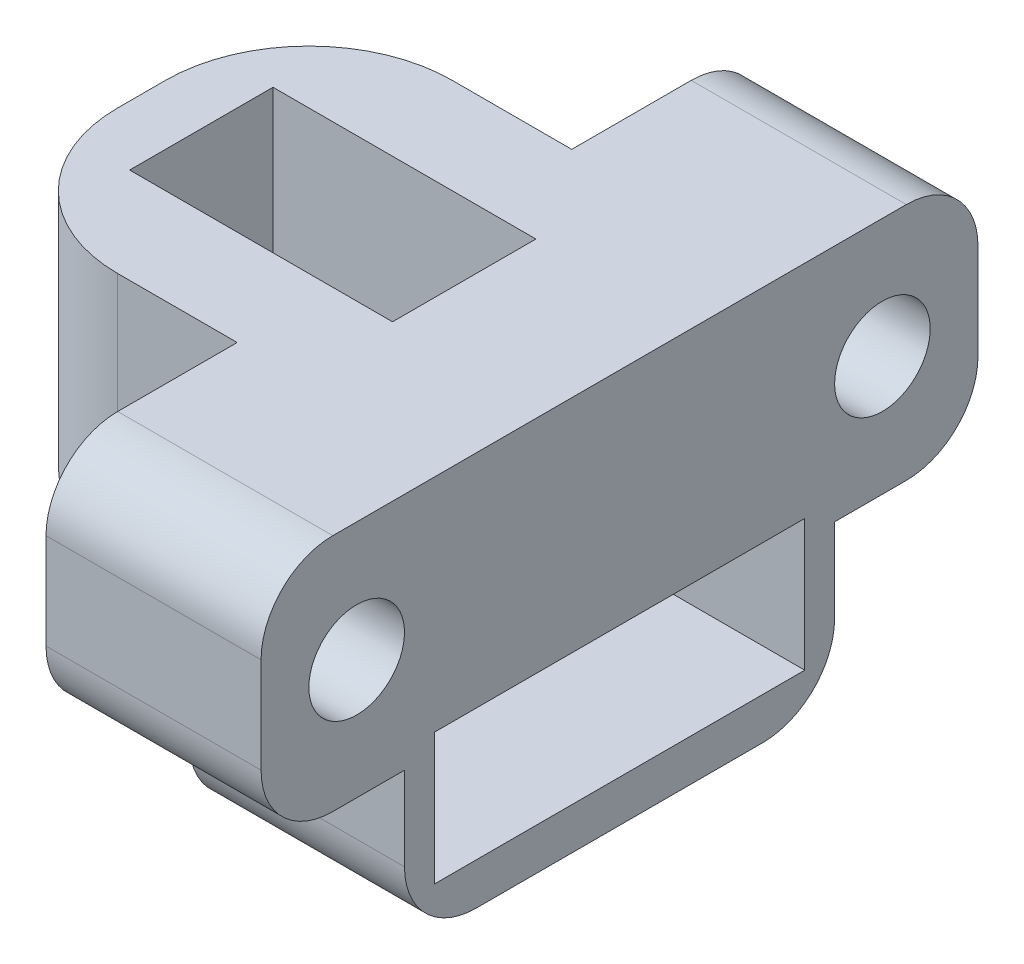
SolidWorks part; units mm, degrees
ref_plane "Plano frontal" through (0, 0, 0) normal (0, 0, 1) x (1, 0, 0)
ref_plane "Plano superior" through (0, 0, 0) normal (0, 1, 0) x (1, 0, 0)
ref_plane "Plano direito" through (0, 0, 0) normal (1, 0, 0) x (0, 0, -1)
sketch "Esboço1" plane through (0, 0, 0) normal (0, 1, 0) x (1, 0, 0)
  line L1 (-10, 15) -> (10, 15)
  line L2 (-10, 15) -> (-10, -15)
  line L3 (-10, -15) -> (10, -15)
  line L4 (10, 15) -> (10, -15)
  line L5 (-10, 15) -> (10, -15) construction
  line L6 (-10, -15) -> (10, 15) construction
  point P0 (0, 0)
  dimension "D1" = 30
  dimension "D2" = 20
extrude "Ressalto-extrusão1" add sketch "Esboço1" along normal blind 10
sketch "Esboço2" plane through (0, 10, 0) normal (0, 1, 0) x (1, 0, 0)
  line L1 (-10, 15) -> (1, 15)
  line L2 (-10, 15) -> (-10, 7)
  line L3 (-10, 7) -> (1, 7)
  line L4 (1, 15) -> (1, 7)
  line L5 (-10, -15) -> (1, -15)
  line L6 (-10, -15) -> (-10, -7)
  line L7 (-10, -7) -> (1, -7)
  line L8 (1, -15) -> (1, -7)
  dimension "D1" = 8
  dimension "D2" = 8
  dimension "D3" = 11
  dimension "D4" = 11
extrude "Corte-extrusão1" cut sketch "Esboço2" against normal blind 10
sketch "Esboço3" plane through (0, 10, 0) normal (0, 1, 0) x (1, 0, 0)
  line L0 (10, 0) -> (3.5, 0) construction
  line L1 (10, -15) -> (10, 15) construction
  line L2 (3.5, 0) -> (3.5, 3) construction
  line L4 (3.5, 3) -> (-7.5, 3)
  line L5 (3.5, 3) -> (3.5, -3)
  line L6 (3.5, -3) -> (-7.5, -3)
  line L7 (-7.5, 3) -> (-7.5, -3)
  dimension "D1" = 6.5
  dimension "D2" = 3
  dimension "D3" = 11
  dimension "D4" = 6
extrude "Corte-extrusão2" cut sketch "Esboço3" against normal blind 7
sketch "Esboço4" plane through (0, 0, 0) normal (0, -1, 0) x (1, 0, 0)
  line L0 (10, 0) -> (5.5, 0) construction
  line L1 (10, 15) -> (10, -15) construction
  line L3 (10, 9) -> (1, 9)
  line L4 (10, 9) -> (10, -9)
  line L5 (10, -9) -> (1, -9)
  line L6 (1, 9) -> (1, -9)
  line L7 (10, 9) -> (1, -9) construction
  line L8 (10, -9) -> (1, 9) construction
  dimension "D1" = 4.5
  dimension "D2" = 9
  dimension "D3" = 18
extrude "Ressalto-extrusão2" add sketch "Esboço4" along normal blind 6.5
sketch "Esboço5" plane through (10, 0, 0) normal (1, 0, 0) x (0, 0, -1)
  line L0 (9, 0) -> (-9, 0) construction
  line L1 (0, 0) -> (0, -2) construction
  line L3 (7.75, -4.75) -> (-7.75, -4.75)
  line L4 (7.75, -4.75) -> (7.75, 0.75)
  line L5 (7.75, 0.75) -> (-7.75, 0.75)
  line L6 (-7.75, -4.75) -> (-7.75, 0.75)
  line L7 (7.75, -4.75) -> (-7.75, 0.75) construction
  line L8 (7.75, 0.75) -> (-7.75, -4.75) construction
  dimension "D1" = 2
  dimension "D2" = 5.5
  dimension "D3" = 15.5
extrude "Corte-extrusão3" cut sketch "Esboço5" against normal blind 7.5
sketch "Esboço6" plane through (1, 0, 0) normal (-1, 0, 0) x (0, 0, 1)
  line L0 (-15, 5) -> (-7, 5) construction
  line L1 (-15, 0) -> (-15, 10) construction
  line L2 (-7, 0) -> (-7, 10) construction
  line L3 (15, 5) -> (7, 5) construction
  line L4 (15, 0) -> (15, 10) construction
  line L5 (7, 0) -> (7, 10) construction
  circle A0 centre (11, 5) radius 2
  circle A1 centre (-11, 5) radius 2
  dimension "D1" = 4
  dimension "D2" = 4
extrude "Corte-extrusão4" cut sketch "Esboço6" against normal through all
sketch "Esboço7" plane through (1, 0, 0) normal (-1, 0, 0) x (0, 0, 1)
  circle A0 centre (11, 5) radius 3.5
  circle A1 centre (-11, 5) radius 3.5
  dimension "D1" = 7
  dimension "D2" = 7
extrude "Corte-extrusão5" cut sketch "Esboço7" against normal blind 2
fillet "Filete1" radius 6 2 edges at (-10, 5, -7) (-10, 5, 7)
fillet "Filete2" radius 3 6 edges at (5.5, 10, 15) (5.5, 10, -15) (5.5, 0, -15) (5.5, 0, 15) (5.5, -6.5, 9) (5.5, -6.5, -9)
